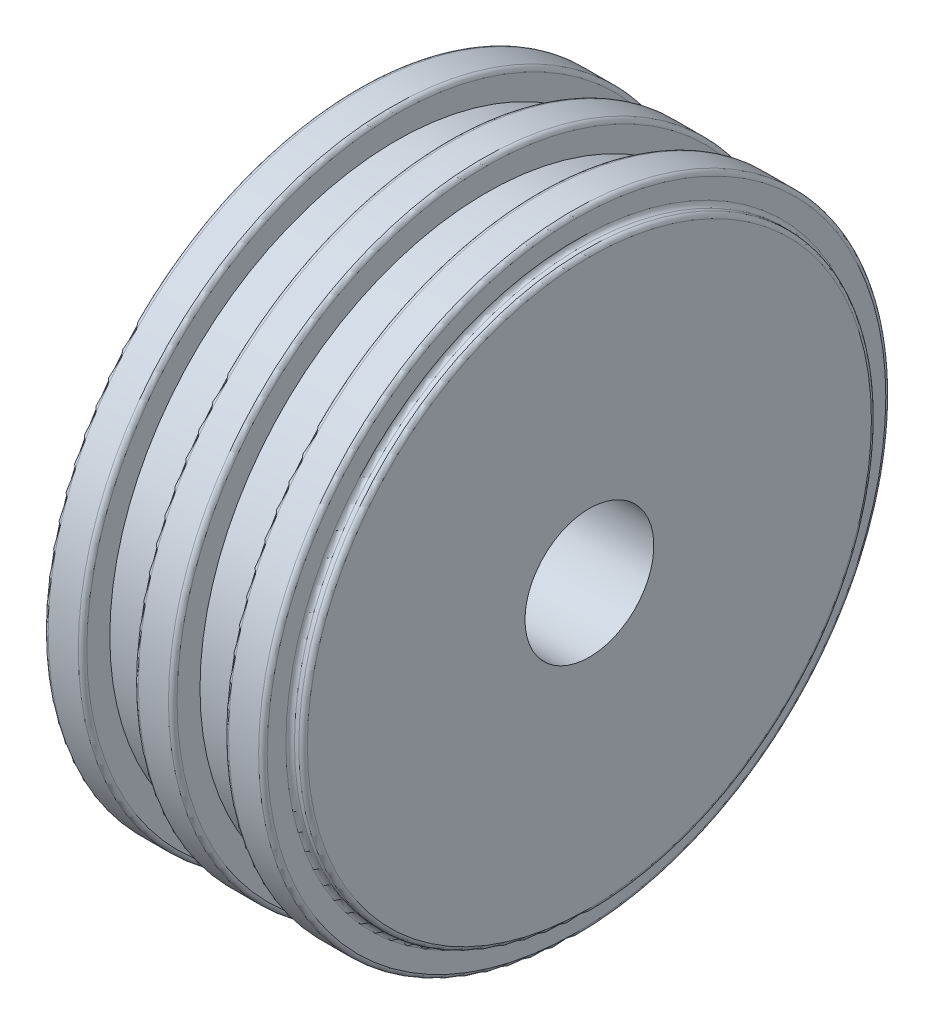
SolidWorks part; units mm, degrees
ref_plane "Front Plane" through (0, 0, 0) normal (0, 0, 1) x (1, 0, 0)
ref_plane "Top Plane" through (0, 0, 0) normal (0, 1, 0) x (1, 0, 0)
ref_plane "Right Plane" through (0, 0, 0) normal (1, 0, 0) x (0, 0, -1)
sketch "Sketch1" plane through (0, 0, 0) normal (0, 0, 1) x (1, 0, 0)
  line L0 (-513.2828, 0) -> (25150.8566, 0) construction
  line L1 (-513.2828, 0) -> (25150.8566, 0) construction
  line L2 (-513.2828, 0) -> (25150.8566, 0) construction
  line L3 (0, 0) -> (0, 25664.1393) construction
  line L4 (0, 15) -> (0, 66.675)
  line L5 (0, 66.675) -> (-3, 66.675)
  line L6 (-3, 66.675) -> (-3, 73.025)
  line L7 (-3, 73.025) -> (-12, 73.025)
  line L8 (-12, 73.025) -> (-12, 66.675)
  line L9 (-12, 66.675) -> (-24, 66.675)
  line L10 (-24, 66.675) -> (-24, 73.025)
  line L11 (-24, 73.025) -> (-33, 73.025)
  line L12 (-33, 73.025) -> (-33, 66.675)
  line L13 (-33, 66.675) -> (-45, 66.675)
  line L14 (-45, 66.675) -> (-45, 73.025)
  line L15 (-45, 73.025) -> (-54, 73.025)
  line L16 (-54, 73.025) -> (-54, 66.675)
  line L17 (-54, 66.675) -> (-57, 66.675)
  line L18 (-57, 66.675) -> (-57, 15)
  line L19 (-57, 15) -> (0, 15)
  dimension "D1" = 30
  dimension "D2" = 133.35
  dimension "D3" = 146.05
  dimension "D4" = 3
  dimension "D5" = 9
  dimension "D6" = 12
revolve "Revolve1" add sketch "Sketch1" angle 360 about L0
fillet "Fillet1" radius 1 10 edges at (-3, 0, 73.025) (-12, 0, 73.025) (-24, 0, 73.025) (-33, 0, 73.025) (-45, 0, 73.025) (-54, 0, 73.025) (-54, 0, 66.675) (-57, 0, 66.675) (0, 0, 66.675) (-3, 0, 66.675)
